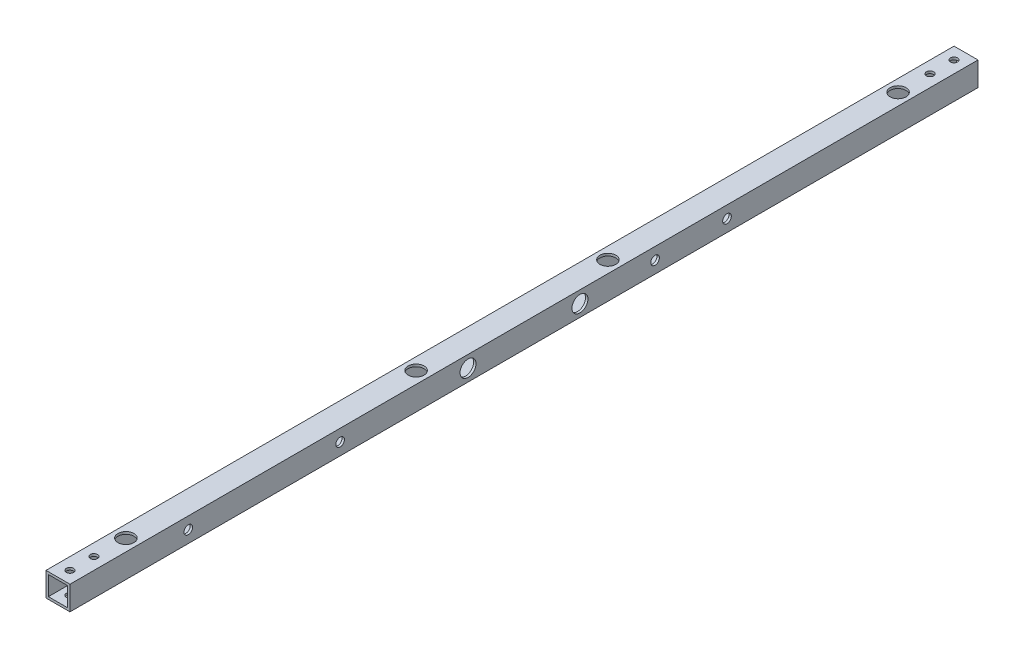
SolidWorks part; units mm, degrees
other "ﾏｰｸｱｯﾌﾟ1"
sketch "ｽｹｯﾁ20" plane through (7.5, 7.5, 568) normal (0.9378, 0.0295, 0.3458) x (-0.1948, -0.7799, 0.5948)
other "ﾏｰｸｱｯﾌﾟ2"
sketch "ｽｹｯﾁ21" plane through (7.5, 7.5, 568) normal (0.9378, 0.0295, 0.3458) x (-0.1948, -0.7799, 0.5948)
material "6063-T5"
ref_plane "正面" through (0, 0, 0) normal (0, 0, 1) x (1, 0, 0)
ref_plane "平面" through (0, 0, 0) normal (0, 1, 0) x (1, 0, 0)
ref_plane "右側面" through (0, 0, 0) normal (1, 0, 0) x (0, 0, -1)
sketch "ｽｹｯﾁ1" plane through (0, 0, 0) normal (0, 0, 1) x (1, 0, 0)
  line L1 (-7.5, -7.5) -> (7.5, -7.5)
  line L2 (-7.5, -7.5) -> (-7.5, 7.5)
  line L3 (-7.5, 7.5) -> (7.5, 7.5)
  line L4 (7.5, -7.5) -> (7.5, 7.5)
  line L5 (-7.5, -7.5) -> (7.5, 7.5) construction
  line L6 (-7.5, 7.5) -> (7.5, -7.5) construction
  line L7 (-6, -6) -> (6, -6)
  line L8 (-6, -6) -> (-6, 6)
  line L9 (-6, 6) -> (6, 6)
  line L10 (6, -6) -> (6, 6)
  line L11 (-6, -6) -> (6, 6) construction
  line L12 (-6, 6) -> (6, -6) construction
  point P0 (0, 0)
  point P6 (0, 0)
  dimension "D1" = 1.5
  dimension "D2" = 15
  dimension "D3" = 15
extrude "ﾎﾞｽ - 押し出し1" add sketch "ｽｹｯﾁ1" along normal blind 568
sketch "ｽｹｯﾁ5" plane through (0, -7.5, 0) normal (0, -1, 0) x (-1, 0, 0)
  line L0 (7.5, 0) -> (-7.5, 0) construction
  line L1 (7.5, -568) -> (7.5, 0) construction
  line L2 (7.5, -568) -> (-7.5, -568) construction
  line L3 (-7.5, -284) -> (7.5, -284) construction
  line L4 (-7.5, -568) -> (-7.5, 0) construction
  circle A0 centre (0, -22.5) radius 2.25
  circle A1 centre (0, -7.5) radius 2.25
  circle A2 centre (0, -560.5) radius 2.25
  circle A3 centre (0, -545.5) radius 2.25
  circle A4 centre (0, -42.5) radius 2.7
  circle A5 centre (0, -224) radius 2.7
  circle A6 centre (0, -344) radius 2.7
  circle A7 centre (0, -525.5) radius 2.7
  dimension "D1" = 7.5
  dimension "D2" = 4.5
  dimension "D3" = 4.5
  dimension "D4" = 15
  dimension "D5" = 7.5
  dimension "D6" = 7.5
  dimension "D8" = 7.5
  dimension "D9" = 5.4
  dimension "D10" = 20
  dimension "D11" = 60
  dimension "D7" = 2
extrude "ｶｯﾄ - 押し出し4" cut sketch "ｽｹｯﾁ5" against normal blind 20
sketch "ｽｹｯﾁ9" plane through (7.5, 0, 0) normal (1, 0, 0) x (0, 0, -1)
  line L0 (-568, -7.5) -> (0, -7.5) construction
  line L1 (-568, 7.5) -> (0, 7.5) construction
  circle A0 centre (-494, 0) radius 2.7
  circle A1 centre (-399, 0) radius 2.7
  circle A2 centre (-202, 0) radius 2.7
  circle A3 centre (-157, 0) radius 2.7
  point P12 (-284, 7.5)
  dimension "D1" = 45
  dimension "D2" = 5.4
  dimension "D3" = 5.4
  dimension "D4" = 7.5
  dimension "D5" = 7.5
  dimension "D6" = 82
  dimension "D7" = 115
  dimension "D9" = 5.4
  dimension "D10" = 5.4
  dimension "D12" = 95
  dimension "D8" = 7.5
  dimension "D11" = 7.5
extrude "ｶｯﾄ - 押し出し6" cut sketch "ｽｹｯﾁ9" against normal blind 40
sketch "ｽｹｯﾁ10" plane through (-7.5, 0, 0) normal (-1, 0, 0) x (0, 0, 1)
  circle A0 centre (157, 0) radius 5
  circle A1 centre (202, 0) radius 5
  circle A2 centre (399, 0) radius 5
  circle A4 centre (494, 0) radius 5
  dimension "D1" = 10
  dimension "D2" = 10
  dimension "D3" = 10
  dimension "D4" = 10
extrude "ｶｯﾄ - 押し出し7" cut sketch "ｽｹｯﾁ10" against normal blind 5
sketch "ｽｹｯﾁ13" plane through (7.5, 0, 0) normal (1, 0, 0) x (0, 0, -1)
  line L0 (-568, 7.5) -> (0, 7.5) construction
  circle A0 centre (-319, 0) radius 2.25
  circle A1 centre (-249, 0) radius 2.25
  point P6 (-284, 7.5)
  dimension "D2" = 7.5
  dimension "D4" = 70
  dimension "D5" = 4.5
  dimension "D6" = 4.5
  dimension "D1" = 7.5
  dimension "D3" = 35
extrude "ｶｯﾄ - 押し出し10" cut sketch "ｽｹｯﾁ13" against normal blind 40
sketch "ｽｹｯﾁ14" plane through (7.5, 0, 0) normal (1, 0, 0) x (0, 0, -1)
  circle A0 centre (-319, 0) radius 5
  circle A1 centre (-249, 0) radius 5
  dimension "D1" = 10
  dimension "D2" = 10
extrude "ｶｯﾄ - 押し出し11" cut sketch "ｽｹｯﾁ14" against normal blind 5
hole_wizard "Ø10.0 (10) 直径の穴1" positions "ｽｹｯﾁ19" profile "ｽｹｯﾁ18" hole size "Ø10.0" standard "JIS"
sketch "ｽｹｯﾁ19" plane through (0, 7.5, 0) normal (0, 1, 0) x (1, 0, 0)
  point P0 (0, -42.5)
  point P3 (0, -224)
  point P6 (0, -344)
  point P9 (0, -525.5)
sketch "ｽｹｯﾁ18" plane through (0, 7.5, 42.5) normal (1, 0, 0) x (0, 0, 1)
  line L0 (0, 0) -> (0, 1.5)
  line L1 (0, 1.5) -> (5, 1.5)
  line L2 (5, 1.5) -> (5, 0)
  line L5 (5, 0) -> (0, 0)
  line L10 (0, 1.5) -> (-5, 1.5) construction
  line L11 (0, -6.35) -> (0, 107.95) construction
  dimension "穴の直径" = 10
  dimension "穴の深さ" = 1.5
  dimension "ﾄﾞﾘﾙ角度" = 180
